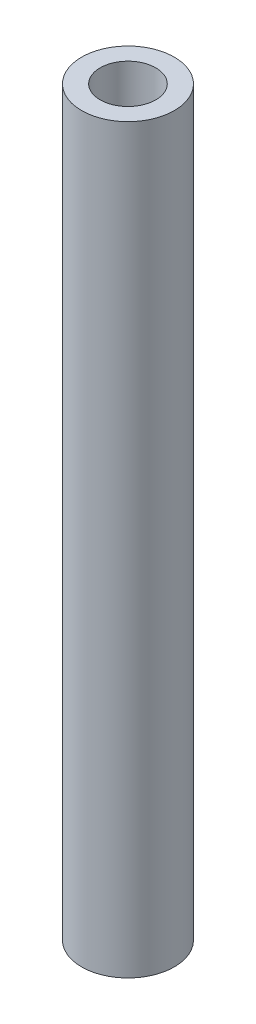
SolidWorks part; units mm, degrees
material "6061 合金"
ref_plane "前视基准面" through (0, 0, 0) normal (0, 0, 1) x (1, 0, 0)
ref_plane "上视基准面" through (0, 0, 0) normal (0, 1, 0) x (1, 0, 0)
ref_plane "右视基准面" through (0, 0, 0) normal (1, 0, 0) x (0, 0, -1)
sketch "草图1" plane through (0, 0, 0) normal (0, 1, 0) x (1, 0, 0)
  circle A0 centre (0, 0) radius 1.5
  circle A1 centre (0, 0) radius 2.5
  dimension "D1" = 3
  dimension "D2" = 5
extrude "凸台-拉伸1" add sketch "草图1" along normal blind 40
